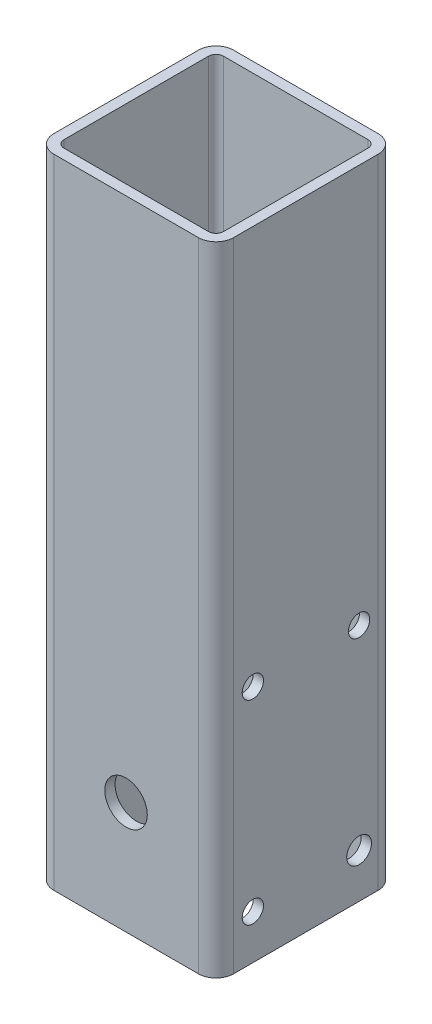
SolidWorks part; units mm, degrees
material "Plain Carbon Steel"
ref_plane "Front Plane" through (0, 0, 0) normal (0, 0, 1) x (1, 0, 0)
ref_plane "Top Plane" through (0, 0, 0) normal (0, 1, 0) x (1, 0, 0)
ref_plane "Right Plane" through (0, 0, 0) normal (1, 0, 0) x (0, 0, -1)
sketch "Sketch1" plane through (0, 0, 0) normal (0, 1, 0) x (1, 0, 0)
  line L0 (-22.5, 20.4) -> (-22.5, -20.4)
  line L1 (-20.4, 25.4) -> (20.4, 25.4)
  line L2 (-25.4, 20.4) -> (-25.4, -20.4)
  line L3 (-20.4, -25.4) -> (20.4, -25.4)
  line L4 (25.4, 20.4) -> (25.4, -20.4)
  line L5 (-25.4, 25.4) -> (25.4, -25.4) construction
  line L6 (-25.4, -25.4) -> (25.4, 25.4) construction
  line L7 (-20.4, -22.5) -> (20.4, -22.5)
  line L8 (22.5, 20.4) -> (22.5, -20.4)
  line L9 (-20.4, 22.5) -> (20.4, 22.5)
  arc A0 (-25.4, -20.4) -> (-20.4, -25.4) centre (-20.4, -20.4) ccw
  arc A1 (20.4, -25.4) -> (25.4, -20.4) centre (20.4, -20.4) ccw
  arc A2 (20.4, 25.4) -> (25.4, 20.4) centre (20.4, 20.4) cw
  arc A3 (-20.4, 25.4) -> (-25.4, 20.4) centre (-20.4, 20.4) ccw
  arc A4 (-22.5, -20.4) -> (-20.4, -22.5) centre (-20.4, -20.4) ccw
  arc A5 (20.4, -22.5) -> (22.5, -20.4) centre (20.4, -20.4) ccw
  arc A6 (20.4, 22.5) -> (22.5, 20.4) centre (20.4, 20.4) cw
  arc A7 (-20.4, 22.5) -> (-22.5, 20.4) centre (-20.4, 20.4) ccw
  point P0 (0, 0)
  dimension "D3" = 5
  dimension "D2" = 50.8
  dimension "D1" = 50.8
  dimension "D4" = 2.9
extrude "Boss-Extrude1" add sketch "Sketch1" along normal blind 180
sketch "Sketch2" plane through (0, 180, 0) normal (0, 1, 0) x (1, 0, 0)
  line L1 (33.1, 25.4) -> (-33.1, 25.4)
  line L2 (38.1, 20.4) -> (38.1, -20.4)
  line L3 (33.1, -25.4) -> (-33.1, -25.4)
  line L4 (-38.1, 20.4) -> (-38.1, -20.4)
  line L5 (38.1, 25.4) -> (-38.1, -25.4) construction
  line L6 (38.1, -25.4) -> (-38.1, 25.4) construction
  line L7 (31.3771, -13.4) -> (-31.3771, -13.4) construction
  line L8 (31.3771, -13.4) -> (31.3771, 13.4) construction
  line L9 (31.3771, 13.4) -> (-31.3771, 13.4) construction
  line L10 (-31.3771, -13.4) -> (-31.3771, 13.4) construction
  line L11 (31.3771, -13.4) -> (-31.3771, 13.4) construction
  line L12 (31.3771, 13.4) -> (-31.3771, -13.4) construction
  arc A0 (-33.1, -25.4) -> (-38.1, -20.4) centre (-33.1, -20.4) cw
  arc A1 (38.1, -20.4) -> (33.1, -25.4) centre (33.1, -20.4) cw
  arc A2 (33.1, 25.4) -> (38.1, 20.4) centre (33.1, 20.4) cw
  arc A3 (-33.1, 25.4) -> (-38.1, 20.4) centre (-33.1, 20.4) ccw
  circle A4 centre (-31.3771, 13.4) radius 4
  circle A5 centre (31.3771, 13.4) radius 4
  circle A6 centre (31.3771, -13.4) radius 4
  circle A7 centre (-31.3771, -13.4) radius 4
  point P0 (0, 0)
  point P18 (0, 0)
  dimension "D3" = 5
  dimension "D4" = 8
  dimension "D5" = 8
  dimension "D6" = 8
  dimension "D7" = 8
  dimension "D8" = 6.7229
  dimension "D1" = 76.2
  dimension "D2" = 50.8
  dimension "D9" = 12
extrude "Boss-Extrude2" [suppressed] add sketch "Sketch2" along normal blind 8
sketch "Sketch3" plane through (-25.4, 0, 0) normal (-1, 0, 0) x (0, 0, 1)
  line L0 (0, 0) -> (0, 40)
  line L1 (-20.4, 0) -> (20.4, 0) construction
  line L2 (-15, 67.5) -> (15, 67.5) construction
  line L3 (-15, 67.5) -> (-15, 12.5) construction
  line L4 (-15, 12.5) -> (15, 12.5) construction
  line L5 (15, 67.5) -> (15, 12.5) construction
  line L6 (-15, 67.5) -> (15, 12.5) construction
  line L7 (-15, 12.5) -> (15, 67.5) construction
  circle A0 centre (-15, 67.5) radius 3
  circle A1 centre (15, 67.5) radius 3
  circle A2 centre (-15, 12.5) radius 3.5
  circle A3 centre (15, 12.5) radius 3
  dimension "D4" = 6
  dimension "D5" = 6
  dimension "D6" = 7
  dimension "D7" = 6
  dimension "D1" = 55
  dimension "D2" = 30
  dimension "D3" = 12.5
extrude "Cut-Extrude1" cut sketch "Sketch3" against normal blind 95 contours A0 | A1 | A2 | A3
sketch "Sketch4" plane through (0, 0, 25.4) normal (0, 0, 1) x (1, 0, 0)
  line L1 (-20.4, 0) -> (20.4, 0) construction
  circle A0 centre (0, 31.67) radius 6
  dimension "D1" = 12
  dimension "D2" = 25.4
  dimension "D3" = 31.67
extrude "Cut-Extrude2" cut sketch "Sketch4" against normal blind 95
equation "\"gantrytubewidth\"=50.8"
equation "\"gantrytuberadius\"= 5"
equation "\"D3@Sketch1\"=\"gantrytuberadius\""
